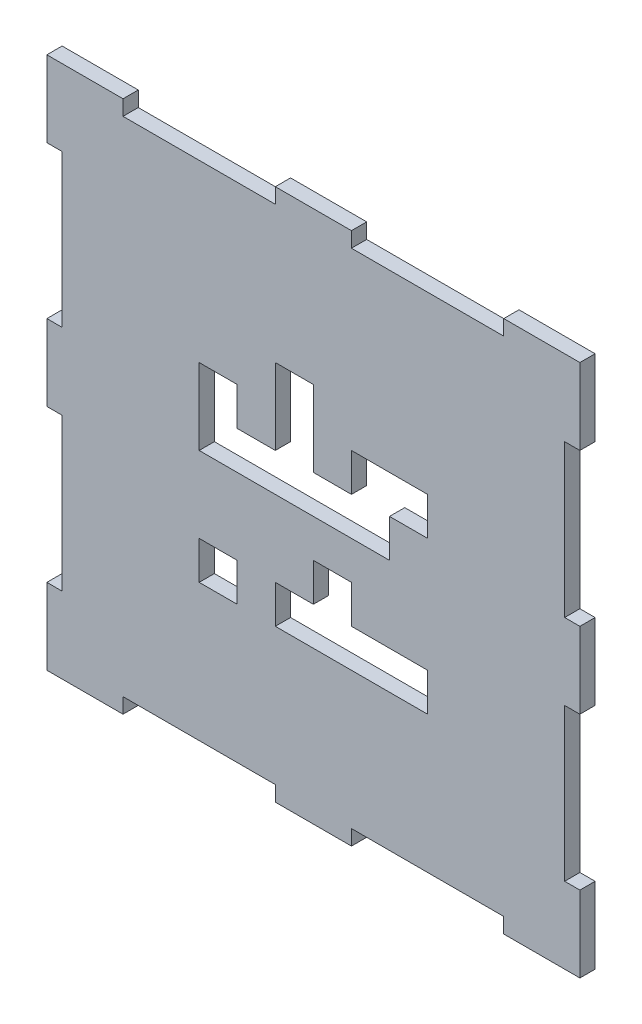
SolidWorks part; units mm, degrees
ref_plane "Front Plane" through (0, 0, 0) normal (0, 0, 1) x (1, 0, 0)
ref_plane "Top Plane" through (0, 0, 0) normal (0, 1, 0) x (1, 0, 0)
ref_plane "Right Plane" through (0, 0, 0) normal (1, 0, 0) x (0, 0, -1)
sketch "Sketch1" plane through (0, 0, 0) normal (0, 0, 1) x (1, 0, 0)
  line L1 (-35, -35) -> (35, -35)
  line L2 (-35, -35) -> (-35, 35)
  line L3 (-35, 35) -> (35, 35)
  line L4 (35, -35) -> (35, 35)
  line L5 (0, 35) -> (0, -35) construction
  line L6 (-35, 0) -> (35, 0) construction
  dimension "D1" = 70
  dimension "D2" = 70
extrude "Boss-Extrude1" add sketch "Sketch1" against normal blind 2
sketch "Sketch2" plane through (0, 0, 0) normal (0, 0, 1) x (1, 0, 0)
  line L0 (-35, 35) -> (-25, 35)
  line L1 (35, 35) -> (-35, 35) construction
  line L2 (-25, 35) -> (-5, 35)
  line L3 (-5, 35) -> (5, 35)
  line L4 (5, 35) -> (25, 35)
  line L6 (35, 35) -> (35, 25)
  line L7 (-25, 33) -> (-5, 33)
  line L8 (-25, 33) -> (-25, 37)
  line L9 (-25, 37) -> (-5, 37)
  line L10 (-5, 33) -> (-5, 37)
  line L11 (-15, 37) -> (-15, 33) construction
  line L12 (-25, 35) -> (-5, 35) construction
  line L13 (5, 33) -> (25, 33)
  line L14 (5, 33) -> (5, 37)
  line L15 (5, 37) -> (25, 37)
  line L16 (25, 33) -> (25, 37)
  line L17 (15, 37) -> (15, 33) construction
  line L18 (5, 35) -> (25, 35) construction
  line L19 (35, -35) -> (35, 35) construction
  line L20 (35, 25) -> (35, 5)
  line L21 (35, 5) -> (35, -5)
  line L22 (35, -5) -> (35, -25)
  line L23 (-35, -35) -> (-25, -35)
  line L24 (35, -5) -> (33, -5)
  line L25 (35, -5) -> (35, -25)
  line L26 (35, -25) -> (33, -25)
  line L27 (33, -5) -> (33, -25)
  line L28 (35, 25) -> (33, 25)
  line L29 (35, 25) -> (35, 5)
  line L30 (35, 5) -> (33, 5)
  line L31 (33, 25) -> (33, 5)
  line L32 (-35, -35) -> (35, -35) construction
  line L33 (-25, -35) -> (-5, -35)
  line L34 (-5, -35) -> (5, -35)
  line L35 (5, -35) -> (25, -35)
  line L36 (-35, 35) -> (-35, 25)
  line L37 (-25, -35) -> (-5, -35)
  line L38 (-25, -35) -> (-25, -33)
  line L39 (-25, -33) -> (-5, -33)
  line L40 (-5, -35) -> (-5, -33)
  line L41 (5, -35) -> (25, -35)
  line L42 (5, -35) -> (5, -33)
  line L43 (5, -33) -> (25, -33)
  line L44 (25, -35) -> (25, -33)
  line L45 (-35, 35) -> (-35, -35) construction
  line L46 (-35, 25) -> (-35, 5)
  line L47 (-35, 5) -> (-35, -5)
  line L48 (-35, -5) -> (-35, -25)
  line L50 (-35, 25) -> (-33, 25)
  line L51 (-35, 25) -> (-35, 5)
  line L52 (-35, 5) -> (-33, 5)
  line L53 (-33, 25) -> (-33, 5)
  line L54 (-35, -5) -> (-33, -5)
  line L55 (-35, -5) -> (-35, -25)
  line L56 (-35, -25) -> (-33, -25)
  line L57 (-33, -5) -> (-33, -25)
  point P7 (15, 35)
  point P9 (-15, 35)
  point P10 (-15, 35)
  point P14 (15, 35)
  line M25 (35, -35) -> (35, 35)
  line M26 (35, 35) -> (-35, 35)
  line M27 (-35, 35) -> (-35, -35)
  line M28 (-35, -35) -> (35, -35)
  dimension "D1" = 10
  dimension "D2" = 20
  dimension "D3" = 10
  dimension "D4" = 20
  dimension "D5" = 4
  dimension "D6" = 20
  dimension "D7" = 20
  dimension "D8" = 4
  dimension "D9" = 10
  dimension "D10" = 20
  dimension "D11" = 10
  dimension "D12" = 20
  dimension "D13" = 2
  dimension "D14" = 2
  dimension "D15" = 10
  dimension "D16" = 20
  dimension "D17" = 10
  dimension "D18" = 20
  dimension "D19" = 20
  dimension "D20" = 20
  dimension "D21" = 2
  dimension "D22" = 2
  dimension "D23" = 10
  dimension "D24" = 20
  dimension "D25" = 10
  dimension "D26" = 20
  dimension "D27" = 2
  dimension "D28" = 2
extrude "Cut-Extrude1" cut sketch "Sketch2" against normal blind 2 contours L53 L50 L52 M27 | L57 L54 L56 M27 | L40 L39 L38 M28 | L44 L43 L42 M28 | L24 L27 L26 M25 | L28 L31 L30 M25 | L13 L16 L14 M26 | L7 L10 L8 M26
sketch "Sketch3" plane through (0, 0, 0) normal (0, 0, 1) x (1, 0, 0)
  line L0 (-15, 20) -> (-15, -20)
  line L1 (-20, -20) -> (20, -20)
  line L2 (-20, -20) -> (-20, 20)
  line L3 (-20, 20) -> (20, 20)
  line L4 (20, -20) -> (20, 20)
  line L5 (0, 20) -> (0, -20) construction
  line L6 (-20, 0) -> (20, 0) construction
  line L7 (-10, 20) -> (-10, -20)
  line L8 (-5, 20) -> (-5, -20)
  line L9 (5, 20) -> (5, -20)
  line L10 (-20, 15) -> (20, 15)
  line L11 (10, 20) -> (10, -20)
  line L12 (15, 20) -> (15, -20)
  line L13 (20, 10) -> (-20, 10)
  line L14 (-20, 5) -> (20, 5)
  line L15 (20, -5) -> (-20, -5)
  line L16 (20, -10) -> (-20, -10)
  line L17 (20, -15) -> (-20, -15)
  line L18 (-20, 0) -> (20, 0)
  line L19 (0, 20) -> (0, -20)
  point P0 (0, 0)
  dimension "D1" = 40
  dimension "D2" = 40
  dimension "D3" = 5
  dimension "D4" = 5
  dimension "D5" = 5
  dimension "D6" = 5
  dimension "D7" = 5
  dimension "D8" = 5
  dimension "D9" = 5
  dimension "D10" = 5
  dimension "D11" = 5
  dimension "D12" = 5
  dimension "D13" = 5
  dimension "D14" = 5
  dimension "D15" = 5
extrude "Cut-Extrude5" cut sketch "Sketch3" against normal blind 10 contours L0 L14 L7 L13 | L0 L18 L7 L14 | L7 L18 L8 L14 | L19 L14 L8 L18 | L14 L19 L18 L9 | L9 L18 L11 L14 | L9 L14 L11 L13 | L11 L14 L12 L13 | L19 L13 L8 L14 | L19 L10 L8 L13 | L17 L7 L16 L0 | L19 L16 L8 L17 | L16 L19 L17 L9 | L17 L11 L16 L9 | L17 L12 L16 L11 | L15 L19 L16 L9
